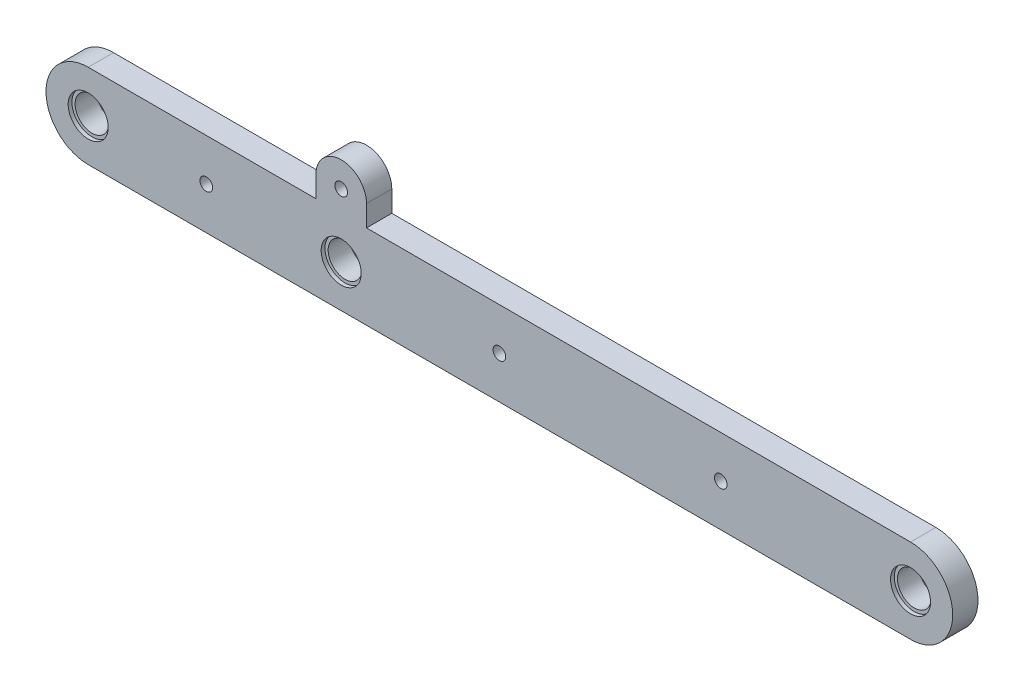
SolidWorks part; units mm, degrees
ref_plane "前视基准面" through (0, 0, 0) normal (0, 0, 1) x (1, 0, 0)
ref_plane "上视基准面" through (0, 0, 0) normal (0, 1, 0) x (1, 0, 0)
ref_plane "右视基准面" through (0, 0, 0) normal (1, 0, 0) x (0, 0, -1)
other "Configuration Table"
sketch "草图1" plane through (0, 0, 0) normal (0, 0, 1) x (1, 0, 0)
  line L3 (-8.9768, 0) -> (15.281, 0) construction
  line L4 (0, 0) -> (135, 0) construction
  line L5 (0, 10) -> (135, 10)
  line L6 (0, -10) -> (135, -10)
  line L7 (0, 0) -> (-60, 0) construction
  line L8 (0, -10) -> (-60, -10)
  line L9 (0, 10) -> (-60, 10)
  line L10 (0, 10) -> (0, 15) construction
  line L11 (-6, 10) -> (-6, 15)
  line L12 (6, 10) -> (6, 15)
  line L13 (67.5, 10) -> (135, 10)
  circle A3 centre (135, 0) radius 4
  circle A4 centre (0, 0) radius 4
  circle A5 centre (-60, 0) radius 4
  arc A6 (0, 10) -> (0, -10) centre (0, 0) ccw
  arc A7 (135, -10) -> (135, 10) centre (135, 0) ccw
  arc A8 (0, -10) -> (0, 10) centre (0, 0) ccw
  arc A9 (-60, 10) -> (-60, -10) centre (-60, 0) ccw
  arc A10 (-6, 10) -> (6, 10) centre (0, 10) ccw
  arc A11 (6, 15) -> (-6, 15) centre (0, 15) ccw
  spline S0 degree 3 poles (-60, 10) (-41.0074, 16.4419) (-10.2231, 26.2095) (55.276, 16.4092) (99.7834, 10.1017) (135, 10) knots 0 0 0 0 0.312279 0.468288 1 1 1 1 construction
  point P9 (67.5, 0)
  point P15 (-30, 0)
  point P25 (0, 12.5)
  dimension "D3" = 8
  dimension "D4" = 8
  dimension "D5" = 8
  dimension "D6" = 10
  dimension "D7" = 10
  dimension "D8" = 6
  dimension "D1" = 135
  dimension "D2" = 60
  dimension "D9" = 5
extrude "凸台-拉伸1" add sketch "草图1" along normal blind 6 contours L9 A9 L8 A6 A5 | A6 A8 A4 | S0 L9 L5 | A6 A10 A8 | A8 A10 L5 | L9 A10 A6
sketch "草图2" plane through (0, 0, 6) normal (0, 0, -1) x (-1, 0, 0)
  point P0 (-135, 0)
  point P3 (60, 0)
  point P6 (0, 0)
hole_wizard "M5 六角头螺栓的柱形沉头孔1" positions "草图2" profile "草图3" counterbore size "M5" standard "GB" end condition through all
sketch "草图3" plane through (135, 0, 6) normal (1, 0, 0) x (0, -1, 0)
  line L0 (0, 0) -> (0, 6)
  line L1 (0, 6) -> (4, 6)
  line L3 (4, 6) -> (4, 0.9)
  line L4 (4, 0.9) -> (4.75, 0.9)
  line L5 (4.75, 0.9) -> (4.75, 0)
  line L7 (4.75, 0) -> (0, 0)
  line L11 (0, -6.35) -> (0, 107.95) construction
  dimension "通孔孔直径" = 8
  dimension "通孔孔深度" = 6
  dimension "柱形沉头孔直径" = 9.5
  dimension "柱形沉头孔深度" = 0.9
sketch "草图7" plane through (0, 0, 0) normal (0, 0, -1) x (-1, 0, 0)
  line L0 (-135, 0) -> (60, 0) construction
  circle A0 centre (-37.5, 0) radius 1.5
  circle A1 centre (-90, 0) radius 1.5
  circle A2 centre (32, 0) radius 1.5
  circle A3 centre (0, 15) radius 1.5
  dimension "D1" = 3
  dimension "D2" = 3
  dimension "D3" = 3
  dimension "D6" = 3
  dimension "D4" = 32
  dimension "D5" = 90
extrude "切除-拉伸1" cut sketch "草图7" against normal through all both and the other way through all
